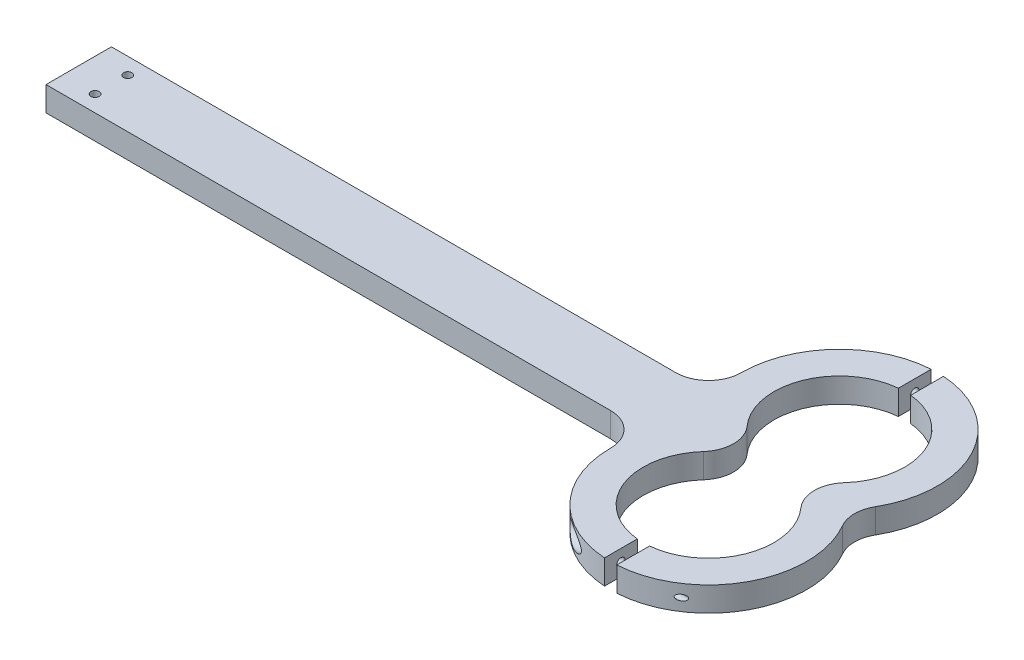
SolidWorks part; units mm, degrees
ref_plane "Front" through (0, 0, 0) normal (0, 0, 1) x (1, 0, 0)
ref_plane "Top" through (0, 0, 0) normal (0, 1, 0) x (1, 0, 0)
ref_plane "Right" through (0, 0, 0) normal (1, 0, 0) x (0, 0, -1)
sketch "Sketch2" plane through (0, 0, 0) normal (0, 1, 0) x (1, 0, 0)
  line L1 (0, 12.7) -> (219.2, 12.7)
  line L2 (0, 12.7) -> (0, -12.7)
  line L3 (0, -12.7) -> (219.2, -12.7)
  line L4 (270, 25.4) -> (270, -25.4) construction
  arc A3 (288.932, 8.4667) -> (251.068, 8.4667) centre (270, 25.4) ccw
  arc A4 (251.068, -8.4667) -> (288.932, -8.4667) centre (270, -25.4) ccw
  arc A6 (231.9, -25.4) -> (302.9956, -6.35) centre (270, -25.4) ccw
  arc A7 (302.9956, 6.35) -> (231.9, 25.4) centre (270, 25.4) ccw
  arc A8 (288.932, 8.4667) -> (288.932, -8.4667) centre (298.3981, 0) ccw
  arc A9 (251.068, 8.4667) -> (251.068, -8.4667) centre (241.6019, 0) cw
  arc A10 (219.2, -12.7) -> (231.9, -25.4) centre (219.2, -25.4) cw
  arc A11 (219.2, 12.7) -> (231.9, 25.4) centre (219.2, 25.4) ccw
  arc A12 (302.9956, 6.35) -> (302.9956, -6.35) centre (313.9941, 0) ccw
  point P4 (0, 0)
  point P10 (270, 0)
  point P21 (234.079, -12.7)
  point P24 (234.079, 12.7)
  dimension "D2" = 270
  dimension "D3" = 12.7
  dimension "D4" = 12.7
  dimension "D5" = 50.8
  dimension "D6" = 12.7
  dimension "D1" = 25.4
extrude "Boss-Extrude1" add sketch "Sketch2" along normal mid plane 9.525
hole_wizard "#4 Clearance Hole1" positions "Sketch12" profile "Sketch13" hole size "#4" standard "ANSI Inch" end condition through all
sketch "Sketch12" plane through (0, -4.7625, 0) normal (0, -1, 0) x (-1, 0, 0)
  point P0 (-12.7, -6.35)
  point P3 (-12.7, 6.35)
sketch "Sketch13" plane through (12.7, -4.7625, 6.35) normal (1, 0, 0) x (0, 0, -1)
  line L0 (0, 0) -> (0, 9.525)
  line L1 (0, 9.525) -> (1.6319, 9.525)
  line L2 (1.6319, 9.525) -> (1.6319, 0)
  line L5 (1.6319, 0) -> (0, 0)
  line L11 (0, -6.35) -> (0, 107.95) construction
  dimension "Thru Hole Dia." = 3.2639
  dimension "Thru Hole Depth" = 9.525
sketch "Sketch14" plane through (0, -4.7625, 0) normal (0, -1, 0) x (1, 0, 0)
  line L0 (267.6188, -50.6881) -> (267.6188, -63.4255)
  line L1 (272.3813, -50.6881) -> (272.3813, -63.4255)
  line L2 (270, -63.5) -> (270, 63.5) construction
  line L3 (267.6188, 50.6881) -> (267.6188, 63.4255)
  line L4 (272.3813, 50.6881) -> (272.3813, 63.4255)
  arc A0 (251.068, -8.4667) -> (288.932, -8.4667) centre (270, -25.4) ccw construction
  arc A1 (231.9, -25.4) -> (302.9956, -6.35) centre (270, -25.4) ccw construction
  arc A2 (302.9956, 6.35) -> (231.9, 25.4) centre (270, 25.4) ccw construction
  arc A3 (267.6188, -50.6881) -> (272.3813, -50.6881) centre (270, -25.4) ccw
  arc A4 (267.6188, -63.4255) -> (272.3813, -63.4255) centre (270, -25.4) ccw
  arc A5 (288.932, 8.4667) -> (251.068, 8.4667) centre (270, 25.4) ccw construction
  arc A6 (272.3813, 63.4255) -> (267.6188, 63.4255) centre (270, 25.4) ccw
  arc A7 (272.3813, 50.6881) -> (267.6188, 50.6881) centre (270, 25.4) ccw
  dimension "D1" = 4.7625
  dimension "D2" = 2.3812
extrude "Cut-Extrude1" cut sketch "Sketch14" against normal through all
ref_plane "Plane1" through (254.3019, 0, 0) normal (1, 0, 0) x (0, 0, -1)
hole_wizard "#4 Clearance Hole2" positions "Sketch20" profile "Sketch21" hole size "#4" standard "ANSI Inch"
sketch "Sketch20" plane through (254.3019, 0, 0) normal (1, 0, 0) x (0, 0, -1)
  line L0 (-63.4255, 4.7625) -> (-50.6881, 4.7625) construction
  line L1 (-63.4255, 4.7625) -> (-63.4255, -4.7625) construction
  point P0 (-57.0568, 0)
  point P6 (-57.0568, 4.7625)
  point P9 (-63.4255, 0)
sketch "Sketch21" plane through (254.3019, 0, 57.0568) normal (0, 1, 0) x (0, 0, 1)
  line L0 (0, 0) -> (0, 18.0783)
  line L1 (0, 18.0783) -> (1.6319, 17.0977)
  line L2 (1.6319, 17.0977) -> (1.6319, 0)
  line L5 (1.6319, 0) -> (0, 0)
  line L10 (0, 18.0783) -> (-1.632, 17.0977) construction
  line L11 (0, -6.35) -> (0, 107.95) construction
  dimension "Hole Dia." = 3.2639
  dimension "Hole Depth" = 18.0783
  dimension "Drill Angle" = 118
sketch "Sketch26" plane through (254.3019, 0, 0) normal (1, 0, 0) x (0, 0, -1)
  circle A5 centre (-57.0568, 0) radius 1.6319 construction
  circle A6 centre (-57.0568, 0) radius 1.6319 construction
  circle A7 centre (-57.0568, 0) radius 3.81
  dimension "D1" = 7.62
extrude "Cut-Extrude2" cut sketch "Sketch26" against normal through all from offset 7.9375
hole_wizard "#4-40 Tapped Hole1" positions "Sketch24" profile "Sketch25" tap size "#4-40" standard "ANSI Inch" end condition through all
sketch "Sketch24" plane through (272.3813, 0, 0) normal (-1, 0, 0) x (0, 0, 1)
  circle A1 centre (57.0568, 0) radius 1.6319 construction
  point P0 (57.0568, 0)
sketch "Sketch25" plane through (272.3813, 0, 57.0568) normal (0, 1, 0) x (0, 0, 1)
  line L0 (0, 0) -> (0, 35.7188)
  line L1 (0, 35.7188) -> (1.1303, 35.7188)
  line L2 (1.1303, 35.7188) -> (1.1303, 0)
  line L5 (1.1303, 0) -> (0, 0)
  line L11 (0, -6.35) -> (0, 107.95) construction
  dimension "Thru Tap Drill Dia." = 2.2606
  dimension "Thru Tap Drill Depth" = 35.7188
cosmetic thread "Hole Thread1" parameters "D2"=2.8448
mirror "Mirror1" about plane through (0, 0, 0) normal (0, 0, 1) of "#4-40 Tapped Hole1", "Cut-Extrude2", "#4 Clearance Hole2"
cosmetic thread "Hole Thread2" parameters "D2"=2.8448
split "Split1" bodies to split 126 125 resulting bodies 127 128
